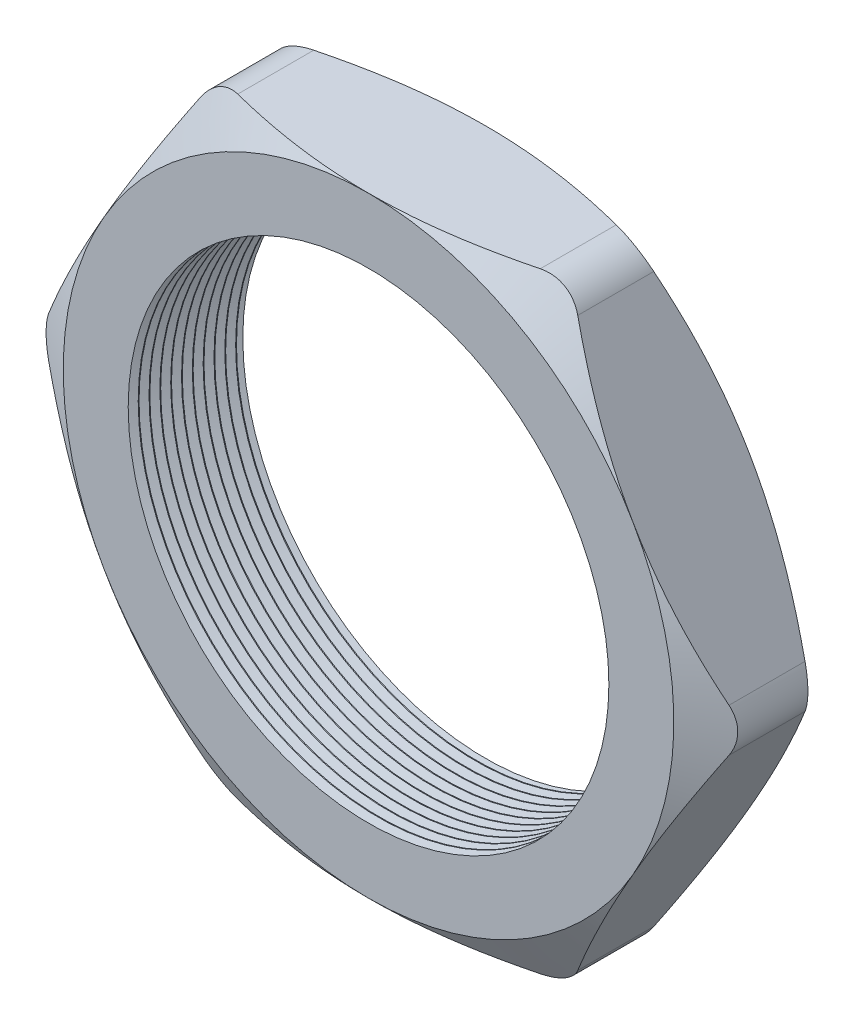
SolidWorks part; units mm, degrees
ref_plane "Front Plane" through (0, 0, 0) normal (0, 0, 1) x (1, 0, 0)
ref_plane "Top Plane" through (0, 0, 0) normal (0, 1, 0) x (1, 0, 0)
ref_plane "Right Plane" through (0, 0, 0) normal (1, 0, 0) x (0, 0, -1)
sketch "Sketch1" plane through (0, 0, 0) normal (0, 0, 1) x (1, 0, 0)
  line L1 (-20.6772, 0) -> (-10.3386, -17.907)
  line L2 (-10.3386, -17.907) -> (10.3386, -17.907)
  line L3 (10.3386, -17.907) -> (20.6772, 0)
  line L4 (20.6772, 0) -> (10.3386, 17.907)
  line L5 (10.3386, 17.907) -> (-10.3386, 17.907)
  line L6 (-10.3386, 17.907) -> (-20.6772, 0)
  circle A0 centre (0, 0) radius 17.907 construction
  circle A1 centre (0, 0) radius 14.097
  dimension "TS" = 28.194
  dimension "H" = 35.814
extrude "Extrude1" add sketch "Sketch1" along normal blind 6.858
sketch "Sketch2" plane through (0, 0, 6.858) normal (0, 0, 1) x (1, 0, 0)
  line L0 (10.3386, 17.907) -> (-10.3386, 17.907) construction
  circle A0 centre (0, 0) radius 17.907
extrude "Cut-Extrude1" cut sketch "Sketch2" against normal through all draft 60 flip side to cut
sketch "Sketch3" plane through (0, 0, 0) normal (0, 0, -1) x (-1, 0, 0)
  line L0 (-10.3386, 17.907) -> (10.3386, 17.907) construction
  circle A0 centre (0, 0) radius 17.907
extrude "Cut-Extrude2" cut sketch "Sketch3" against normal through all draft 60 flip side to cut
fillet "Fillet1" radius 2.54 6 edges at (20.6772, 0, 3.429) (10.3386, -17.907, 3.429) (-10.3386, -17.907, 3.429) (-20.6772, 0, 3.429) (-10.3386, 17.907, 3.429) (10.3386, 17.907, 3.429)
sketch "Sketch4" plane through (0, 0, 0) normal (0, 1, 0) x (1, 0, 0)
  line L0 (-14.097, -6.858) -> (-14.097, -6.2714)
  line L1 (-14.097, 0) -> (-14.097, -6.858) construction
  line L2 (-14.097, -6.2714) -> (-14.605, -6.5647)
  line L3 (-14.605, -6.5647) -> (-14.097, -6.858)
  dimension "D1" = 60
  dimension "D2" = 60
  dimension "D3" = 0.508
revolve "Cut-Revolve1" cut sketch "Sketch4" angle 360 about axis through (0, 0, 0) along (0, 0, 1)
pattern_linear "LPattern1" count 11 spacing 0.635 along (0, 0, -1) of "Cut-Revolve1"
